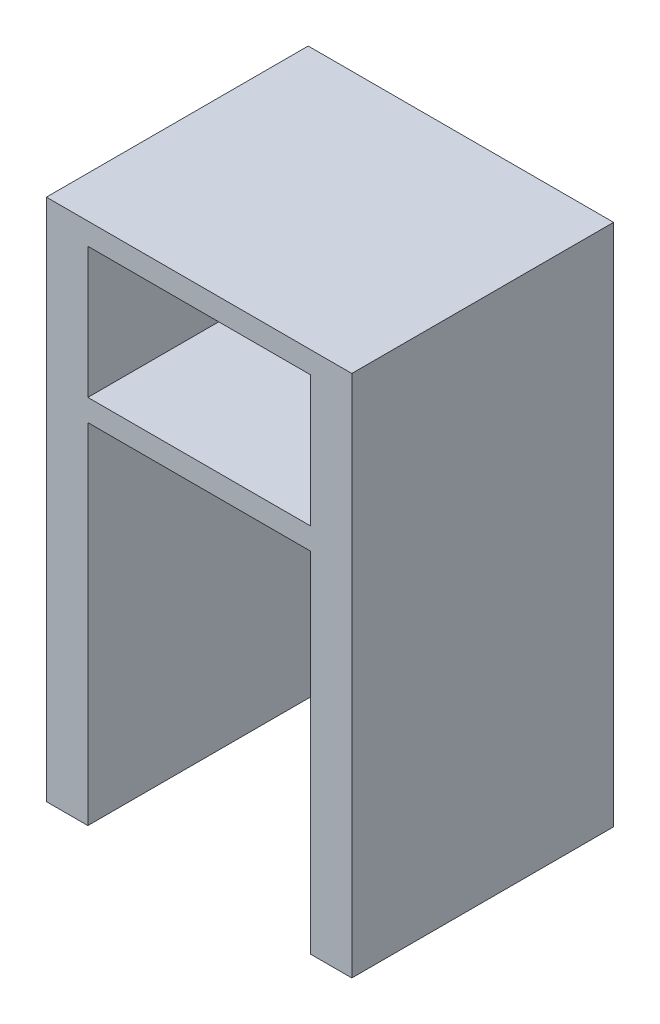
SolidWorks part; units mm, degrees
ref_plane "Piano frontale" through (0, 0, 0) normal (0, 0, 1) x (1, 0, 0)
ref_plane "Piano superiore" through (0, 0, 0) normal (0, 1, 0) x (1, 0, 0)
ref_plane "Piano destro" through (0, 0, 0) normal (1, 0, 0) x (0, 0, -1)
sketch "Schizzo1" plane through (0, 0, 0) normal (0, 0, 1) x (1, 0, 0)
  line L1 (-70, 120) -> (70, 120)
  line L2 (-70, 120) -> (-70, -120)
  line L3 (-70, -120) -> (70, -120)
  line L4 (70, 120) -> (70, -120)
  line L5 (-70, 120) -> (70, -120) construction
  line L6 (-70, -120) -> (70, 120) construction
  point P0 (0, 0)
  dimension "D1" = 140
  dimension "D2" = 240
extrude "Estrusione-Estrusione1" add sketch "Schizzo1" along normal blind 120
sketch "Schizzo2" plane through (0, 0, 120) normal (0, 0, 1) x (1, 0, 0)
  line L0 (-70, -120) -> (70, -120) construction
  line L1 (-51, 40) -> (51, 40)
  line L2 (-51, 40) -> (-51, -120)
  line L3 (-51, -120) -> (51, -120)
  line L4 (51, 40) -> (51, -120)
  line L6 (-51, 110) -> (51, 110)
  line L7 (-51, 110) -> (-51, 50)
  line L8 (-51, 50) -> (51, 50)
  line L9 (51, 110) -> (51, 50)
  point P6 (0, 40)
  dimension "D1" = 102
  dimension "D2" = 160
  dimension "D3" = 170
  dimension "D4" = 60
extrude "Taglio-Estrusione1" cut sketch "Schizzo2" against normal blind 120
